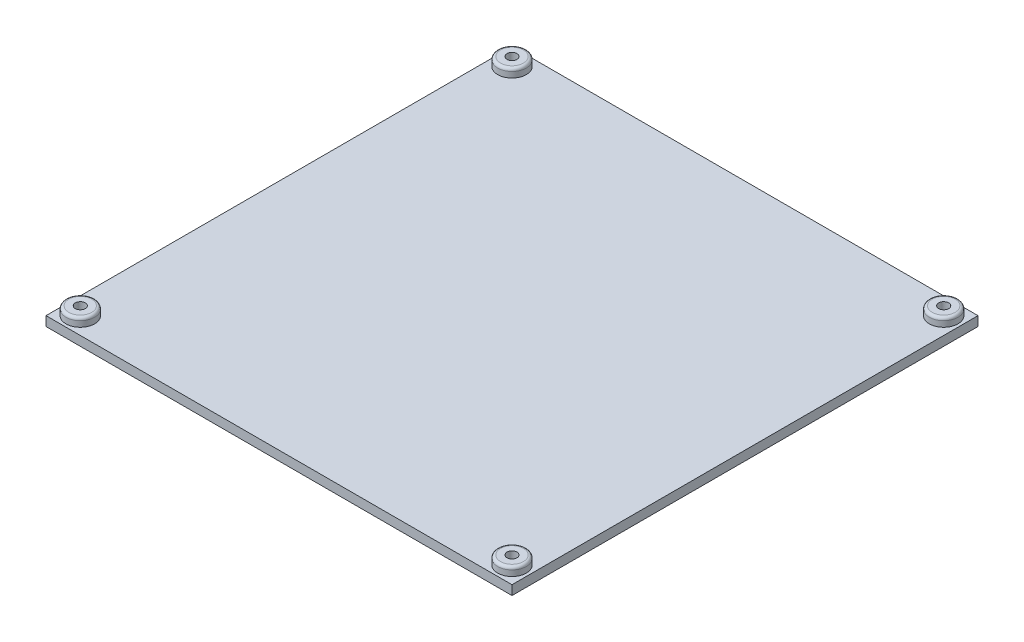
SolidWorks part; units mm, degrees
ref_plane "Alzado" through (0, 0, 0) normal (0, 0, 1) x (1, 0, 0)
ref_plane "Planta" through (0, 0, 0) normal (0, 1, 0) x (1, 0, 0)
ref_plane "Vista lateral" through (0, 0, 0) normal (1, 0, 0) x (0, 0, -1)
sketch "Croquis1" plane through (0, 0, 0) normal (0, 1, 0) x (1, 0, 0)
  line L1 (-81.5, 81.5) -> (81.5, 81.5)
  line L2 (-81.5, 81.5) -> (-81.5, -81.5)
  line L3 (-81.5, -81.5) -> (81.5, -81.5)
  line L4 (81.5, 81.5) -> (81.5, -81.5)
  line L5 (-81.5, 81.5) -> (81.5, -81.5) construction
  line L6 (-81.5, -81.5) -> (81.5, 81.5) construction
  line L7 (-75.5, 75.5) -> (75.5, 75.5) construction
  line L8 (-75.5, 75.5) -> (-75.5, -75.5) construction
  line L9 (-75.5, -75.5) -> (75.5, -75.5) construction
  line L10 (75.5, 75.5) -> (75.5, -75.5) construction
  line L11 (-75.5, 75.5) -> (75.5, -75.5) construction
  line L12 (-75.5, -75.5) -> (75.5, 75.5) construction
  point P0 (0, 0)
  point P6 (0, 0)
  dimension "D1" = 163
  dimension "D2" = 163
  dimension "D3" = 151
extrude "Saliente-Extruir1" add sketch "Croquis1" against normal blind 3.3
sketch "Croquis2" plane through (0, 0, 0) normal (0, 1, 0) x (1, 0, 0)
  circle A0 centre (-75.5, 75.5) radius 5
  circle A1 centre (75.5, 75.5) radius 5
  circle A2 centre (-75.5, -75.5) radius 5
  circle A3 centre (75.5, -75.5) radius 5
  dimension "D1" = 10
  dimension "D2" = 10
  dimension "D3" = 10
  dimension "D4" = 10
extrude "Saliente-Extruir2" add sketch "Croquis2" along normal blind 3
fillet "Redondeo1" radius 1 4 edges at (75.5, 3, -70.5) (75.5, 3, 80.5) (-75.5, 3, 80.5) (-75.5, 3, -70.5)
sketch "Croquis3" plane through (0, -3.3, 0) normal (0, -1, 0) x (1, 0, 0)
  circle A0 centre (-75.5, 75.5) radius 3.25
  circle A1 centre (75.5, 75.5) radius 3.25
  circle A2 centre (-75.5, -75.5) radius 3.25
  circle A3 centre (75.5, -75.5) radius 3.25
  dimension "D1" = 6.5
  dimension "D2" = 6.5
  dimension "D3" = 6.5
  dimension "D4" = 6.5
extrude "Cortar-Extruir1" cut sketch "Croquis3" against normal blind 3
sketch "Croquis4" plane through (0, 3, 0) normal (0, 1, 0) x (1, 0, 0)
  circle A0 centre (75.5, -75.5) radius 1.75
  circle A1 centre (75.5, 75.5) radius 1.75
  circle A2 centre (-75.5, 75.5) radius 1.75
  circle A3 centre (-75.5, -75.5) radius 1.75
  dimension "D1" = 3.5
  dimension "D2" = 3.5
  dimension "D3" = 3.5
  dimension "D4" = 3.5
extrude "Cortar-Extruir2" cut sketch "Croquis4" against normal up to surface (6.3 mm away) up to face at (75.5, -3.3, 72.25)
